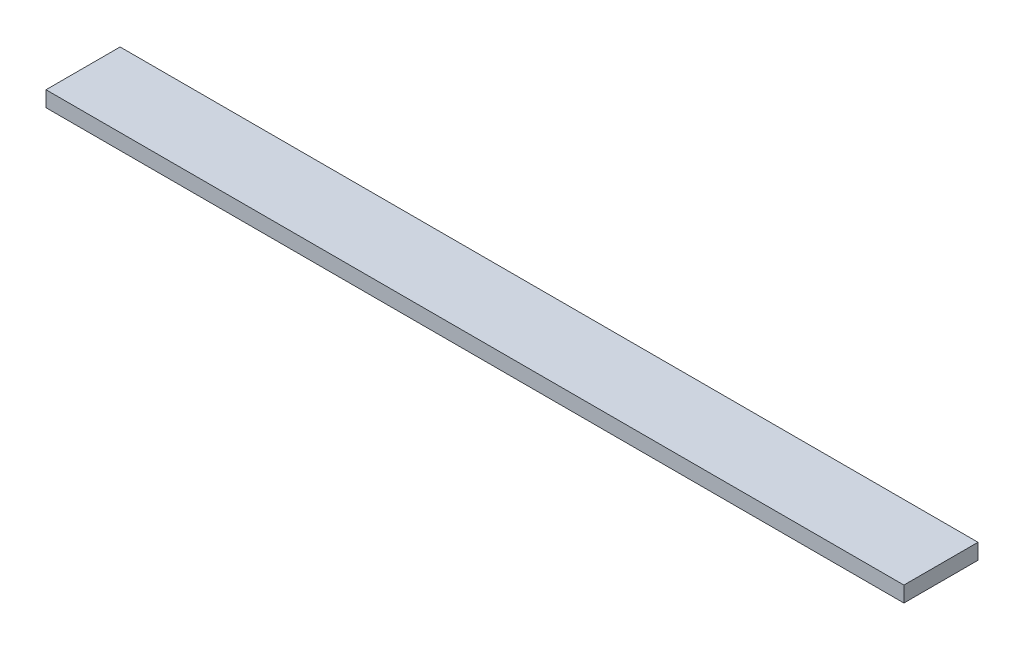
SolidWorks part; units mm, degrees
ref_plane "Front Plane" through (0, 0, 0) normal (0, 0, 1) x (1, 0, 0)
ref_plane "Top Plane" through (0, 0, 0) normal (0, 1, 0) x (1, 0, 0)
ref_plane "Right Plane" through (0, 0, 0) normal (1, 0, 0) x (0, 0, -1)
sketch "Sketch1" plane through (0, 0, 0) normal (0, 1, 0) x (1, 0, 0)
  line L1 (0, 0) -> (139.7, 0)
  line L2 (0, 0) -> (0, 12.065)
  line L3 (0, 12.065) -> (139.7, 12.065)
  line L4 (139.7, 0) -> (139.7, 12.065)
  dimension "D1" = 12.065
  dimension "D2" = 139.7
extrude "Boss-Extrude1" add sketch "Sketch1" along normal blind 2.54
